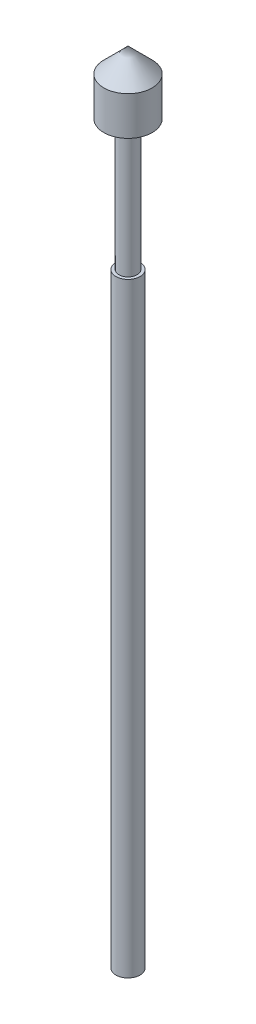
SolidWorks part; units mm, degrees
ref_plane "Front Plane" through (0, 0, 0) normal (0, 0, 1) x (1, 0, 0)
ref_plane "Top Plane" through (0, 0, 0) normal (0, 1, 0) x (1, 0, 0)
ref_plane "Right Plane" through (0, 0, 0) normal (1, 0, 0) x (0, 0, -1)
sketch "Sketch1" plane through (0, 0, 0) normal (0, 0, 1) x (1, 0, 0)
  line L0 (0, 0) -> (0, 33)
  line L1 (0, 33) -> (1, 32)
  line L2 (1, 32) -> (1, 30.4)
  line L3 (1, 30.4) -> (0.375, 30.4)
  line L4 (0.375, 30.4) -> (0.375, 25)
  line L5 (0.375, 25) -> (0.5, 25)
  line L6 (0.5, 25) -> (0.5, 0)
  line L7 (0.5, 0) -> (0, 0)
  dimension "D1" = 33
  dimension "D2" = 0.5
  dimension "D3" = 25
  dimension "D4" = 1
  dimension "D5" = 0.375
  dimension "D6" = 45
  dimension "D7" = 2.6
revolve "Revolve1" add sketch "Sketch1" angle 360 about L0
